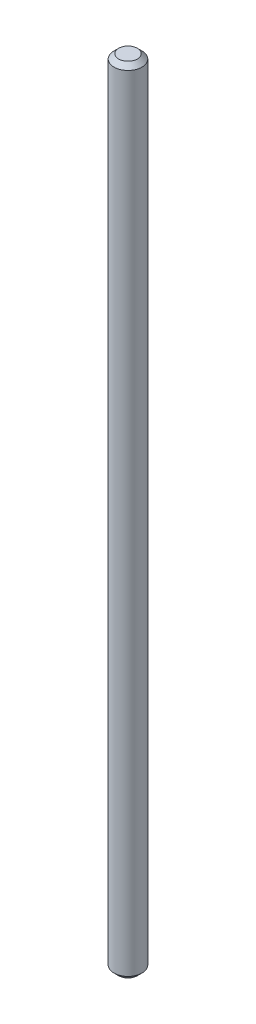
SolidWorks part; units mm, degrees
material "AISI 1035 Steel (SS)"
ref_plane "Front Plane" through (0, 0, 0) normal (0, 0, 1) x (1, 0, 0)
ref_plane "Top Plane" through (0, 0, 0) normal (0, 1, 0) x (1, 0, 0)
ref_plane "Right Plane" through (0, 0, 0) normal (1, 0, 0) x (0, 0, -1)
sketch "Sketch2" plane through (0, 0, 0) normal (0, 1, 0) x (1, 0, 0)
  circle A0 centre (0, 0) radius 1.5
  dimension "D1" = 3
extrude "Boss-Extrude1" add sketch "Sketch2" along normal blind 85
chamfer "Chamfer1" distance 0.5 angle 45 2 edges at (0, 85, 1.5) (0, 0, 1.5)
